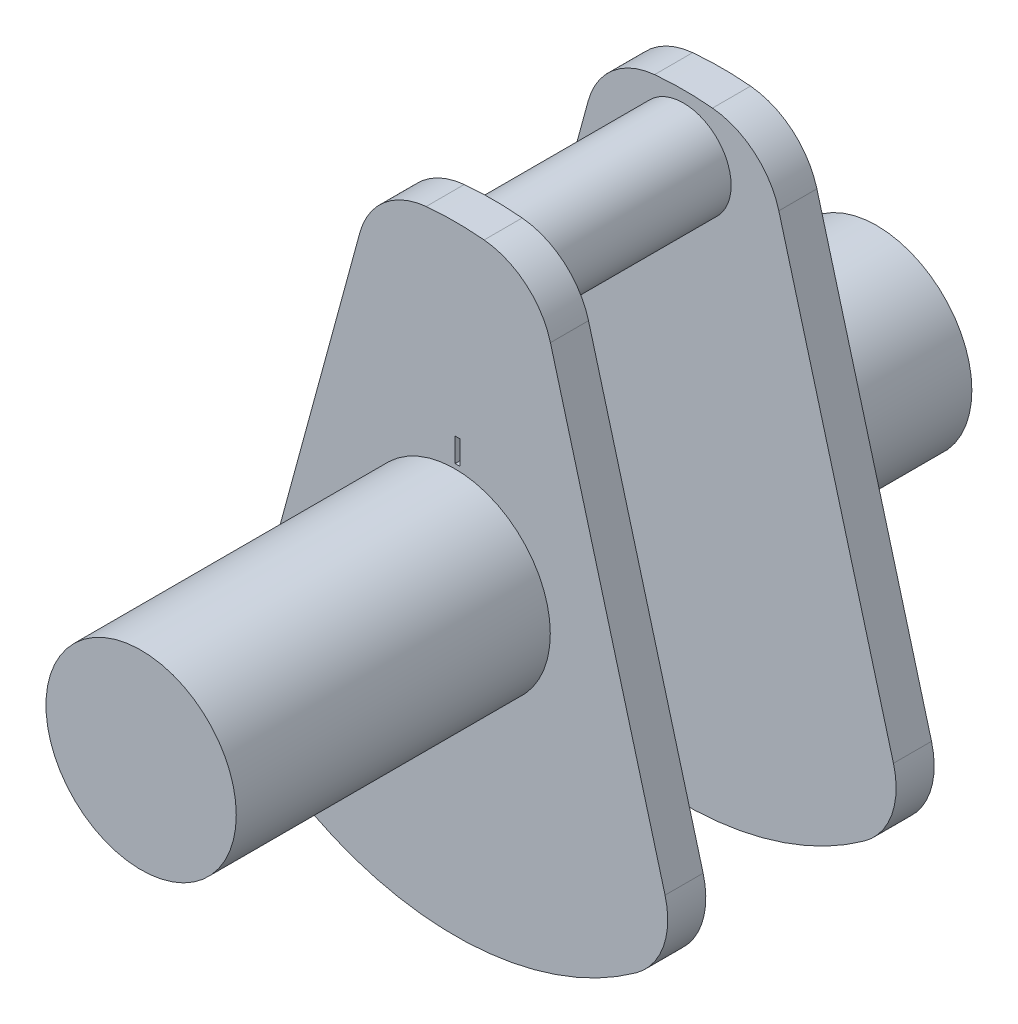
SolidWorks part; units mm, degrees
ref_plane "Front Plane" through (0, 0, 0) normal (0, 0, 1) x (1, 0, 0)
ref_plane "Top Plane" through (0, 0, 0) normal (0, 1, 0) x (1, 0, 0)
ref_plane "Right Plane" through (0, 0, 0) normal (1, 0, 0) x (0, 0, -1)
sketch "Sketch1" plane through (0, 0, 0) normal (0, 0, 1) x (1, 0, 0)
  line L0 (0, 65) -> (0, -65) construction
  line L1 (-20.0284, 52.9863) -> (-44.1187, -35.5279)
  line L2 (20.0284, 52.9863) -> (44.1187, -35.5279)
  arc A0 (-38.0452, -52.7026) -> (38.0452, -52.7026) centre (0, 0) ccw
  arc A1 (6.0888, 64.7142) -> (-6.0888, 64.7142) centre (0, 0) ccw
  arc A2 (20.0284, 52.9863) -> (6.0888, 64.7142) centre (4.59, 48.7845) ccw
  arc A3 (-20.0284, 52.9863) -> (-6.0888, 64.7142) centre (-4.59, 48.7845) cw
  arc A4 (44.1187, -35.5279) -> (38.0452, -52.7026) centre (28.6802, -39.7296) cw
  arc A5 (-44.1187, -35.5279) -> (-38.0452, -52.7026) centre (-28.6802, -39.7296) ccw
  point P12 (17.4047, 62.6265)
  point P15 (-17.4047, 62.6265)
  point P18 (46.7424, -45.168)
  point P21 (-46.7424, -45.168)
  dimension "D1" = 130
  dimension "D4" = 16
  dimension "D5" = 16
  dimension "D2" = 30.45
  dimension "D3" = 9.18
extrude "Boss-Extrude1" add sketch "Sketch1" along normal blind 8
sketch "Sketch2" plane through (0, 0, 8) normal (0, 0, 1) x (1, 0, 0)
  line L0 (0, 65) -> (0, 52.59) construction
  arc A0 (6.0888, 64.7142) -> (-6.0888, 64.7142) centre (0, 0) ccw construction
  circle A1 centre (0, 52.59) radius 10
  dimension "D1" = 20
  dimension "D2" = 52.59
extrude "Boss-Extrude2" add sketch "Sketch2" along normal blind 20
sketch "Sketch3" plane through (0, 0, 0) normal (0, 0, -1) x (-1, 0, 0)
  circle A0 centre (0, 0) radius 20
  dimension "D1" = 40
extrude "Boss-Extrude3" add sketch "Sketch3" along normal blind 32.6
mirror "Mirror1" about plane through (0, 52.59, 28) normal (0, 0, 1) of bodies 103
sketch "Sketch4" plane through (0, 0, 88.6) normal (0, 0, 1) x (1, 0, 0)
  circle A1 centre (0, 0) radius 20
  circle A2 centre (0, 0) radius 20
  dimension "D1" = 0
extrude "Boss-Extrude4" add sketch "Sketch4" along normal blind 33.4
scale "Scale1" bodies to scale 105 scale about centroid uniform scaling yes scale factor 0.1
sketch "Sketch5" plane through (0, 0, 41.725) normal (0, 0, 1) x (1, 0, 0)
  line L0 (0, 0) -> (0, 3.209) construction
  line L2 (0, 1.5017) -> (0.1, 1.5017)
  line L3 (0, 1.5017) -> (0, 1.0017)
  line L4 (0, 1.0017) -> (0.1, 1.0017)
  line L5 (0.1, 1.5017) -> (0.1, 1.0017)
  dimension "D1" = 0.1
  dimension "D2" = 0.5
extrude "Cut-Extrude1" cut sketch "Sketch5" against normal blind 0.1
